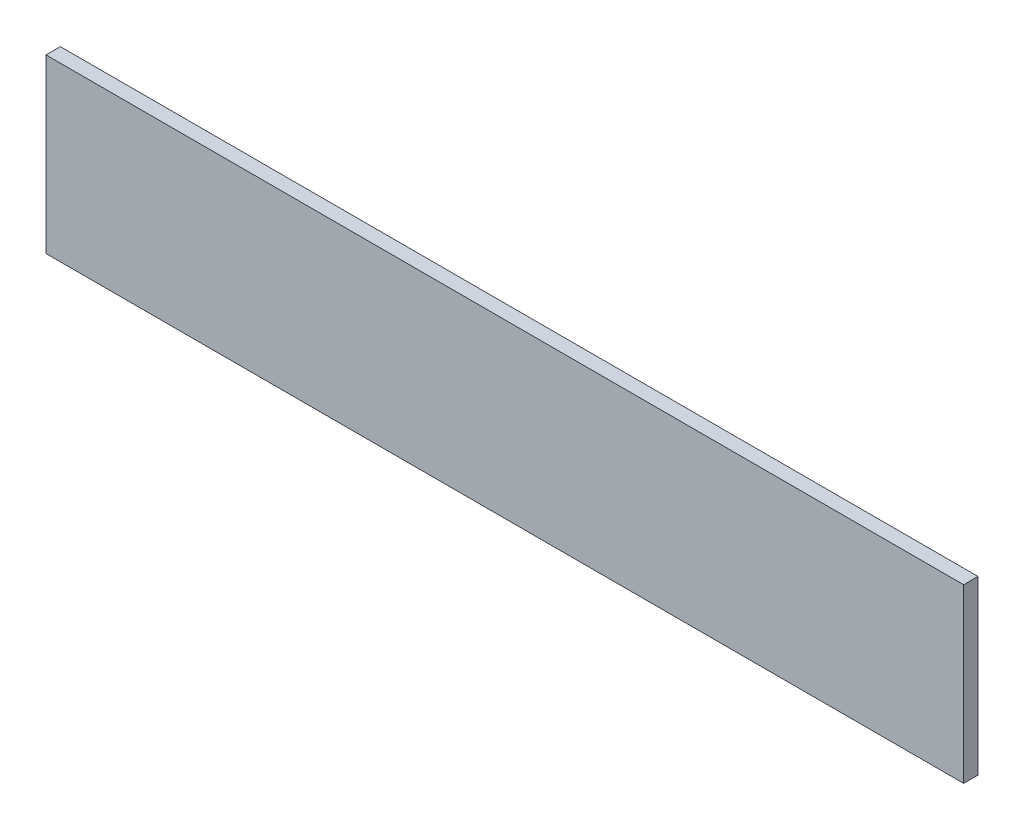
SolidWorks part; units mm, degrees
ref_plane "Front Plane" through (0, 0, 0) normal (0, 0, 1) x (1, 0, 0)
ref_plane "Top Plane" through (0, 0, 0) normal (0, 1, 0) x (1, 0, 0)
ref_plane "Right Plane" through (0, 0, 0) normal (1, 0, 0) x (0, 0, -1)
sketch "Sketch1" plane through (0, 0, 0) normal (0, 0, 1) x (1, 0, 0)
  line L1 (0, 0) -> (406.4, 0)
  line L2 (0, 0) -> (0, 76.2)
  line L3 (0, 76.2) -> (406.4, 76.2)
  line L4 (406.4, 0) -> (406.4, 76.2)
  dimension "D1" = 76.2
  dimension "D2" = 406.4
extrude "Boss-Extrude1" add sketch "Sketch1" along normal blind 6.35
